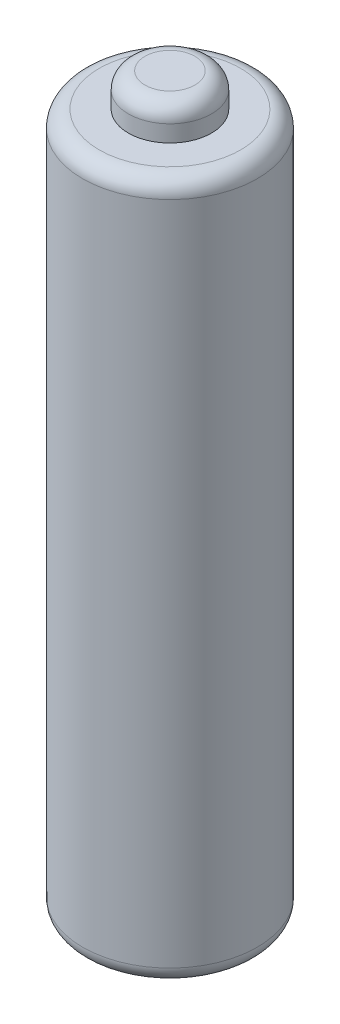
SolidWorks part; units mm, degrees
material "1060 Alloy"
ref_plane "Front Plane" through (0, 0, 0) normal (0, 0, 1) x (1, 0, 0)
ref_plane "Top Plane" through (0, 0, 0) normal (0, 1, 0) x (1, 0, 0)
ref_plane "Right Plane" through (0, 0, 0) normal (1, 0, 0) x (0, 0, -1)
sketch "Sketch1" plane through (0, 0, 0) normal (0, 1, 0) x (1, 0, 0)
  circle A0 centre (0, 0) radius 5.25
extrude "Boss-Extrude1" add sketch "Sketch1" along normal blind 42
sketch "Sketch2" plane through (0, 42, 0) normal (0, 1, 0) x (1, 0, 0)
  circle A0 centre (0, 0) radius 2.5
extrude "Boss-Extrude2" add sketch "Sketch2" along normal blind 2
fillet "Fillet1" radius 1 3 edges at (0, 44, 2.5) (0, 0, 5.25) (0, 42, 5.25)
